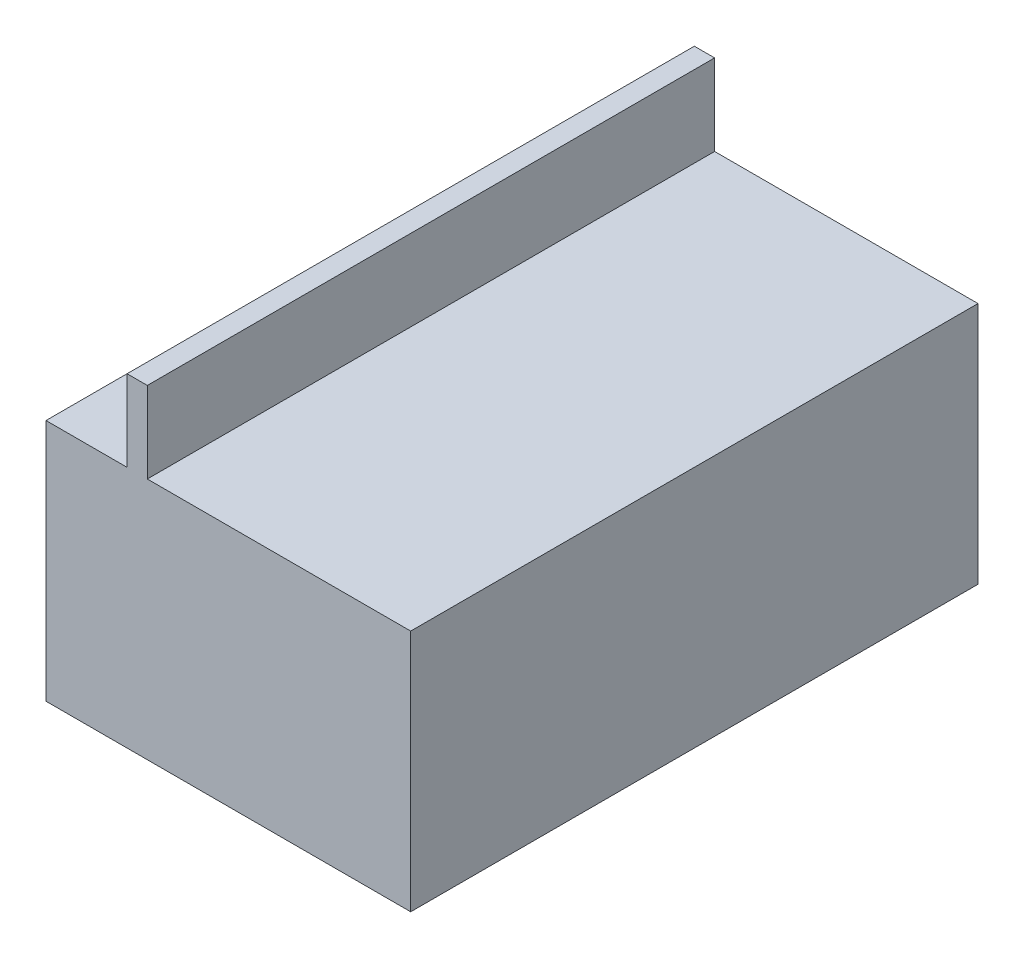
SolidWorks part; units mm, degrees
ref_plane "Front Plane" through (0, 0, 0) normal (0, 0, 1) x (1, 0, 0)
ref_plane "Top Plane" through (0, 0, 0) normal (0, 1, 0) x (1, 0, 0)
ref_plane "Right Plane" through (0, 0, 0) normal (1, 0, 0) x (0, 0, -1)
sketch "Sketch1" plane through (0, 0, 0) normal (0, 1, 0) x (1, 0, 0)
  line L1 (0, 0) -> (90, 0)
  line L2 (0, 0) -> (0, -140)
  line L3 (0, -140) -> (90, -140)
  line L4 (90, 0) -> (90, -140)
  dimension "D1" = 90
  dimension "D2" = 140
extrude "Boss-Extrude1" add sketch "Sketch1" along normal blind 60
sketch "Sketch2" plane through (0, 60, 0) normal (0, 1, 0) x (1, 0, 0)
  line L0 (90, 0) -> (0, 0) construction
  line L1 (20, 0) -> (25, 0)
  line L2 (20, 0) -> (20, -140)
  line L3 (20, -140) -> (25, -140)
  line L4 (25, 0) -> (25, -140)
  line L5 (0, -140) -> (90, -140) construction
  line L6 (0, 0) -> (0, -140) construction
  dimension "D1" = 5
  dimension "D2" = 20
extrude "Boss-Extrude2" add sketch "Sketch2" along normal blind 20
